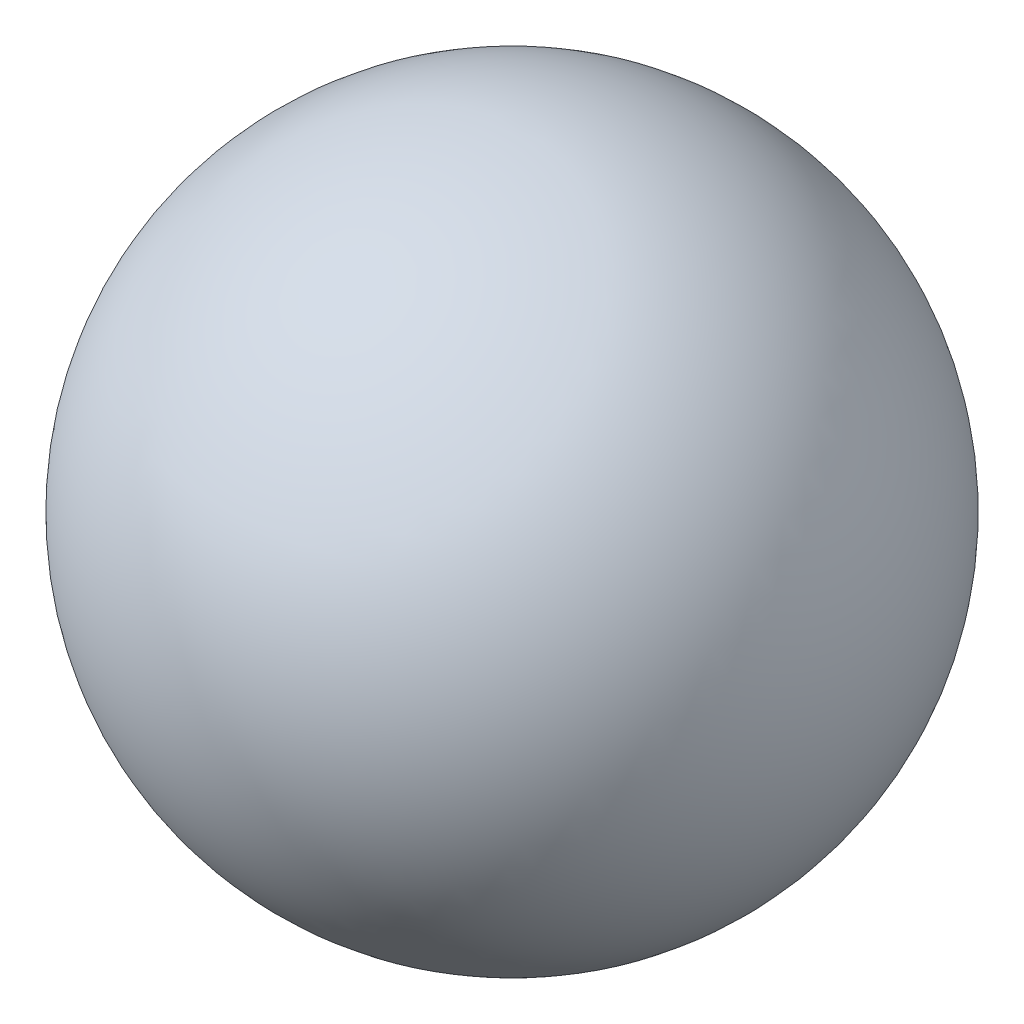
SolidWorks part; units mm, degrees
ref_plane "Plan de face" through (0, 0, 0) normal (0, 0, 1) x (1, 0, 0)
ref_plane "Plan de dessus" through (0, 0, 0) normal (0, 1, 0) x (1, 0, 0)
ref_plane "Plan de droite" through (0, 0, 0) normal (1, 0, 0) x (0, 0, -1)
sketch "Esquisse1" plane through (0, 0, 0) normal (0, 0, 1) x (1, 0, 0)
  line L0 (0, 11.11) -> (0, -11.11)
  arc A0 (0, 11.11) -> (0, -11.11) centre (0, 0) ccw
  dimension "D1" = 22.22
revolve "Révolution3" add sketch "Esquisse1" angle 360 about L0
